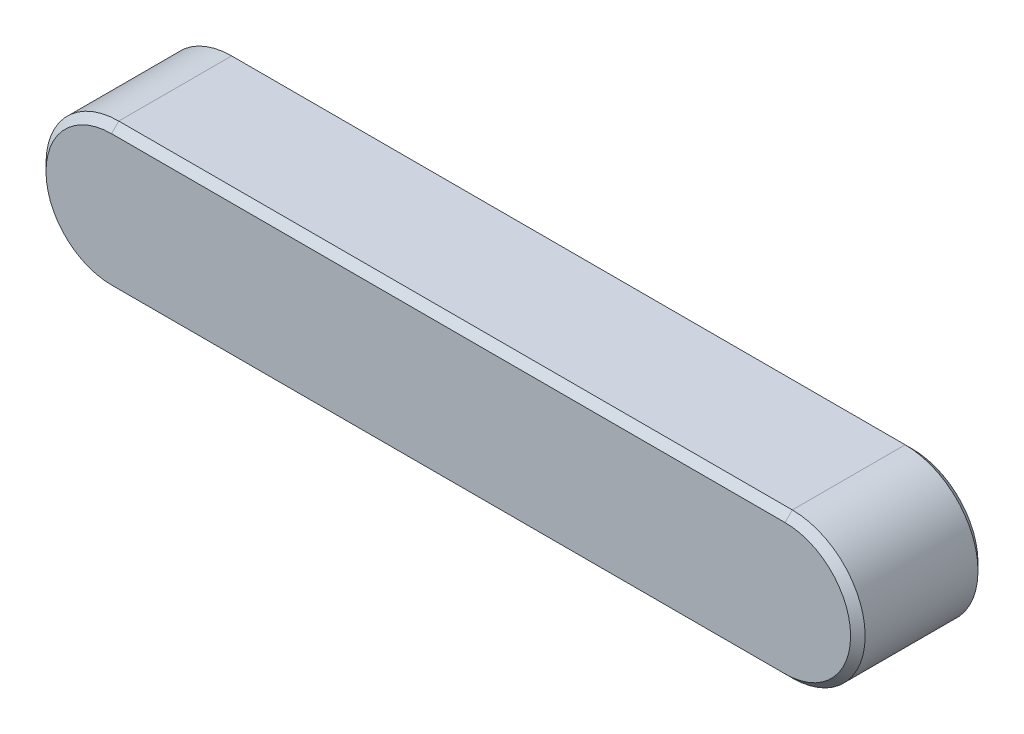
SolidWorks part; units mm, degrees
ref_plane "Front" through (0, 0, 0) normal (0, 0, 1) x (1, 0, 0)
ref_plane "Top" through (0, 0, 0) normal (0, 1, 0) x (1, 0, 0)
ref_plane "Right" through (0, 0, 0) normal (1, 0, 0) x (0, 0, -1)
sketch "Sketch1" plane through (0, 0, 0) normal (0, 0, 1) x (1, 0, 0)
  line L0 (-37, 4) -> (0, 4)
  line L1 (0, -4) -> (-37, -4)
  arc A0 (0, 4) -> (0, -4) centre (0, 0) cw
  arc A1 (-37, -4) -> (-37, 4) centre (-37, 0) cw
  dimension "L" = 45
  dimension "b" = 8
extrude "BaseKey" add sketch "Sketch1" along normal mid plane 7
sketch "Sketch2" plane through (0, 0, 0) normal (0, 0, 1) x (1, 0, 0)
  line L1 (-41, 4) -> (4, 4)
  line L2 (-41, 4) -> (-41, -4)
  line L3 (-41, -4) -> (4, -4)
  line L4 (4, 4) -> (4, -4)
  line L6 (0, -4) -> (-37, -4) construction
  line L7 (-37, 4) -> (0, 4) construction
  arc A2 (0, -4) -> (0, 4) centre (0, 0) ccw construction
  arc A3 (-37, 4) -> (-37, -4) centre (-37, 0) ccw construction
extrude "Extrude1" [suppressed] add sketch "Sketch2" along normal mid plane 7
sketch "Sketch3" plane through (0, 0, 0) normal (0, 0, 1) x (1, 0, 0)
  line L0 (4, 4) -> (-37, 4)
  line L1 (-37, -4) -> (4, -4)
  line L2 (4, -4) -> (4, 4)
  line L5 (-37, 4) -> (0, 4) construction
  arc A0 (-37, 4) -> (-37, -4) centre (-37, 0) ccw
  arc A1 (0, -4) -> (0, 4) centre (0, 0) ccw construction
  arc A4 (-37, 4) -> (-37, -4) centre (-37, 0) ccw construction
extrude "Extrude2" [suppressed] add sketch "Sketch3" along normal mid plane 7
chamfer "Chamfer1" distance 0.4 angle 45 8 edges at (4, 0, -3.5) (-18.5, -4, -3.5) (-41, 0, -3.5) (-18.5, 4, -3.5) (-41, 0, 3.5) (-18.5, -4, 3.5) (4, 0, 3.5) (-18.5, 4, 3.5)
equation "\"D1@Extrude1\"=\"h@BaseKey\""
equation "\"D1@Extrude2\"=\"h@BaseKey\""
